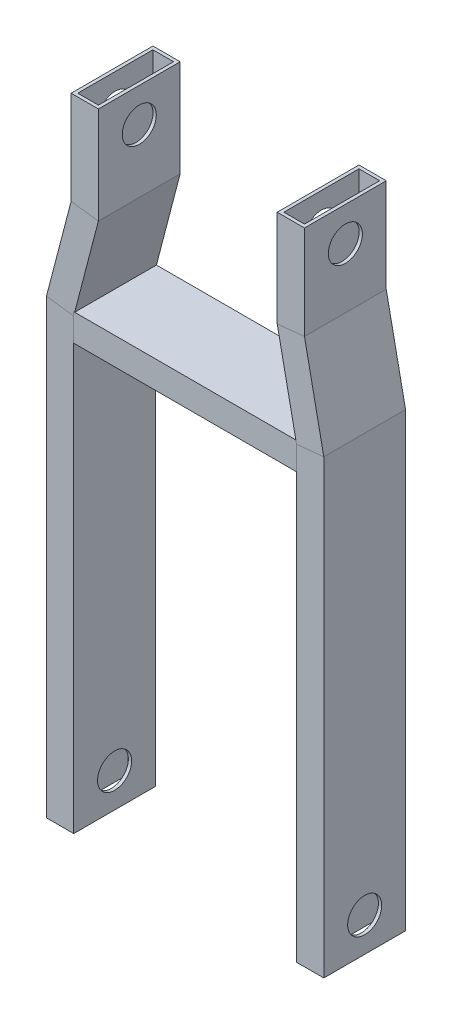
SolidWorks part; units mm, degrees
other "DetailItem3"
other "DetailItem4"
other "DetailItem5"
other "DetailItem6"
other "DetailItem7"
other "DetailItem8"
other "Weld Folder"
other "Weld Bead3"
other "Weld Bead4"
other "Weld Bead5"
other "Weld Bead6"
other "Weld Bead7"
other "Weld Bead8"
material "A500"
ref_plane "Front Plane" through (0, 0, 0) normal (0, 0, 1) x (1, 0, 0)
ref_plane "Top Plane" through (0, 0, 0) normal (0, 1, 0) x (1, 0, 0)
ref_plane "Right Plane" through (0, 0, 0) normal (1, 0, 0) x (0, 0, -1)
sketch3d "3DSketch2"
  line L0 (0, 0, 0) -> (0, 520, 0) construction
  line L1 (0, 0, 0) -> (0, 419.45, 0)
  line L2 (0, 419.45, 0) -> (119.05, 419.45, 0) construction
  line L3 (119.05, 419.45, 0) -> (233.1, 419.45, 0) construction
  line L4 (233.1, 419.45, 0) -> (233.1, 0, 0)
  line L5 (0, 419.45, 0) -> (0, 408.59, 0)
  line L6 (23, 596.45, 0) -> (215.1, 596.45, 0) construction
  line L7 (119.05, 419.45, 0) -> (119.05, 596.45, 0) construction
  line L8 (23, 596.45, 0) -> (23, 507.55, 0)
  line L9 (23, 507.55, 0) -> (0, 419.45, 0)
  line L10 (215.1, 596.45, 0) -> (215.1, 507.55, 0)
  line L11 (215.1, 507.55, 0) -> (233.1, 419.45, 0)
  line L12 (0, 408.59, 0) -> (233.1, 408.59, 0)
  point P10 (119.05, 419.45, 0)
  point P11 (119.05, 596.45, 0)
  point P16 (0, 0, 0)
  point P17 (0, 0, 0)
  dimension "D3" = 119.05
  dimension "D1" = 520
  dimension "D2" = 419.45
  dimension "D4" = 114.05
  dimension "D5" = 10.86
  dimension "D6" = 192.1
  dimension "D7" = 177
  dimension "D8" = 88.9
other "Steel 3X1(1)"
ref_plane "Plane1" through (215.1, 596.45, 0) normal (0, -1, 0) x (1, 0, 0)
sketch "Sketch1" plane through (215.1, 596.45, 0) normal (0, -1, 0) x (1, 0, 0)
  line L1 (-12.7, -38.1) -> (12.7, -38.1)
  line L2 (-12.7, -38.1) -> (-12.7, 38.1)
  line L3 (-12.7, 38.1) -> (12.7, 38.1)
  line L4 (12.7, -38.1) -> (12.7, 38.1)
  line L5 (-12.7, -38.1) -> (12.7, 38.1) construction
  line L6 (-12.7, 38.1) -> (12.7, -38.1) construction
  line L7 (-9.652, -35.052) -> (9.652, -35.052)
  line L8 (-9.652, -35.052) -> (-9.652, 35.052)
  line L9 (-9.652, 35.052) -> (9.652, 35.052)
  line L10 (9.652, -35.052) -> (9.652, 35.052)
  line L11 (-9.652, -35.052) -> (9.652, 35.052) construction
  line L12 (-9.652, 35.052) -> (9.652, -35.052) construction
  point P0 (0, 0)
  point P6 (0, 0)
  point P11 (0, 0)
  dimension "D1" = 76.2
  dimension "D2" = 25.4
  dimension "D3" = 3.048
  dimension "D4" = 3.048
sketch "Sketch3" plane through (245.8, 0, 0) normal (1, 0, 0) x (0, 0, -1)
  line L0 (0, 0) -> (0, 31.75)
  line L1 (0, 0) -> (0, 419.45) construction
  circle A0 centre (0, 31.75) radius 15.875
  dimension "D2" = 31.75
  dimension "D1" = 31.75
extrude "Cut-Extrude1" cut sketch "Sketch3" against normal through all
sketch "Sketch4" plane through (227.8, 0, 0) normal (1, 0, 0) x (0, 0, -1)
  line L0 (0, 596.45) -> (0, 564.7)
  line L1 (0, 596.45) -> (0, 507.55) construction
  circle A0 centre (0, 564.7) radius 15.875
  point P6 (0, 520)
  point P7 (0, 520)
  point P8 (0, 0)
  point P11 (0, 0)
  dimension "D2" = 31.75
  dimension "D1" = 31.75
extrude "Cut-Extrude2" cut sketch "Sketch4" against normal through all
equation "\"D3@3DSketch2\"=100mm + 0.75in"
equation "\"D4@3DSketch2\"=95mm + 0.75in"
equation "\"D6@3DSketch2\"=217.5mm - 1in"
